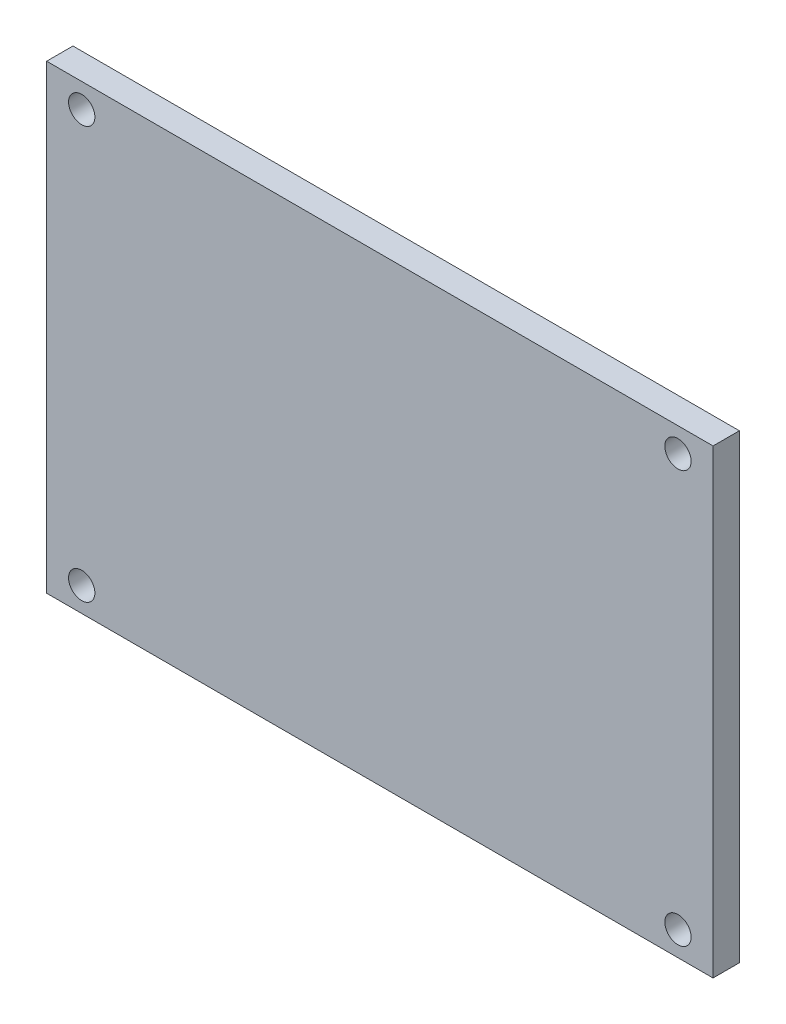
SolidWorks part; units mm, degrees
material "PCB"
ref_plane "Front Plane" through (0, 0, 0) normal (0, 0, 1) x (1, 0, 0)
ref_plane "Top Plane" through (0, 0, 0) normal (0, 1, 0) x (1, 0, 0)
ref_plane "Right Plane" through (0, 0, 0) normal (1, 0, 0) x (0, 0, -1)
sketch "Sketch1" plane through (0, 0, 0) normal (0, 0, 1) x (1, 0, 0)
  line L1 (0, 0) -> (76, 0)
  line L2 (0, 0) -> (0, 52.55)
  line L3 (0, 52.55) -> (76, 52.55)
  line L4 (76, 0) -> (76, 52.55)
  dimension "D1" = 76
  dimension "D2" = 52.55
extrude "Boss-Extrude1" add sketch "Sketch1" along normal blind 3
sketch "Sketch2" plane through (0, 0, 3) normal (0, 0, 1) x (1, 0, 0)
  line L0 (0, 26.275) -> (4, 26.275) construction
  line L1 (4, 49.775) -> (72, 49.775)
  line L2 (4, 49.775) -> (4, 2.775)
  line L3 (4, 2.775) -> (72, 2.775)
  line L4 (72, 49.775) -> (72, 2.775)
  line L5 (0, 52.55) -> (0, 0) construction
  line L6 (38, 52.55) -> (38, 49.775) construction
  line L7 (76, 52.55) -> (0, 52.55) construction
  circle A0 centre (4, 49.775) radius 1.5
  circle A1 centre (72, 49.775) radius 1.5
  circle A2 centre (72, 2.775) radius 1.5
  circle A3 centre (4, 2.775) radius 1.5
  dimension "D3" = 3
  dimension "D1" = 68
  dimension "D2" = 47
extrude "Cut-Extrude1" cut sketch "Sketch2" against normal through all contours A0 | A1 | A2 | A3
